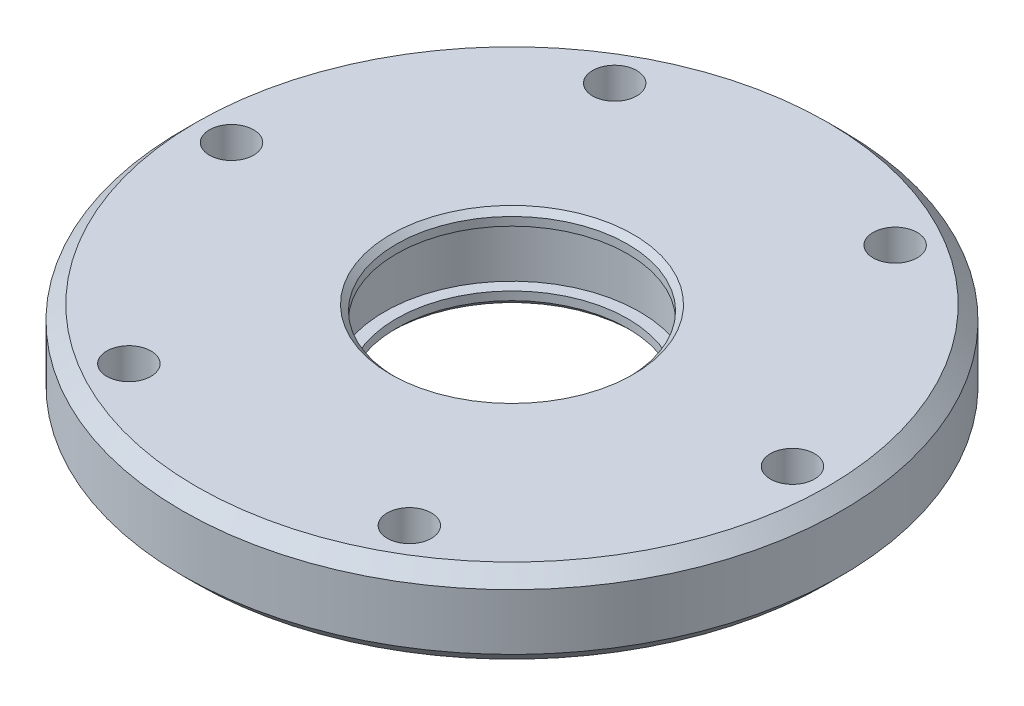
SolidWorks part; units mm, degrees
ref_plane "Front Plane" through (0, 0, 0) normal (0, 0, 1) x (1, 0, 0)
ref_plane "Top Plane" through (0, 0, 0) normal (0, 1, 0) x (1, 0, 0)
ref_plane "Right Plane" through (0, 0, 0) normal (1, 0, 0) x (0, 0, -1)
sketch "Sketch1" plane through (0, 0, 0) normal (0, 1, 0) x (1, 0, 0)
  circle A0 centre (0, 0) radius 20 construction
  circle A1 centre (20, 0) radius 1.575
  circle A2 centre (10, -17.3205) radius 1.575
  circle A3 centre (-10, -17.3205) radius 1.575
  circle A4 centre (-20, 0) radius 1.575
  circle A5 centre (-10, 17.3205) radius 1.575
  circle A6 centre (10, 17.3205) radius 1.575
  circle A7 centre (0, 0) radius 23.5
  circle A8 centre (0, 0) radius 8.25
  point P17 (0, 0)
  dimension "D1" = 40
  dimension "D2" = 3.15
  dimension "D5" = 16.5
  dimension "D4" = 3.5
  dimension "D3" = 6
extrude "Boss-Extrude1" add sketch "Sketch1" along normal mid plane 6
sketch "Sketch2" plane through (0, 0, 0) normal (0, 1, 0) x (1, 0, 0)
  circle A0 centre (0, 0) radius 9.1
  dimension "D1" = 18.2
extrude "Cut-Extrude1" cut sketch "Sketch2" against normal mid plane 4
sketch "Sketch3" plane through (0, -3, 0) normal (0, 1, 0) x (1, 0, 0)
  circle A0 centre (0, 0) radius 18.425
  circle A1 centre (0, 0) radius 21.575
  circle A2 centre (10, 17.3205) radius 1.575 construction
extrude "Boss-Extrude2" add sketch "Sketch3" along normal blind 1
sketch "Sketch4" [suppressed] plane through (0, -3, 0) normal (0, -1, 0) x (1, 0, 0)
  circle A0 centre (0, 0) radius 17.5
  circle A2 centre (0, 0) radius 3.75
  dimension "D1" = 35
  dimension "D2" = 7.5
extrude "Boss-Extrude3" [suppressed] add sketch "Sketch4" along normal blind 10
sketch "Sketch5" [suppressed] plane through (0, -3, 0) normal (0, -1, 0) x (1, 0, 0)
  circle A0 centre (0, 0) radius 19
  circle A1 centre (0, 0) radius 17.5 construction
  circle A2 centre (0, 0) radius 17.5
  dimension "D1" = 1.5
extrude "Boss-Extrude4" [suppressed] add sketch "Sketch5" along normal blind 0.5
chamfer "Chamfer1" distance 1 angle 45 2 edges at (0, -3, 23.5) (0, 3, 23.5)
chamfer "Chamfer2" distance 0.4 angle 45 2 edges at (0, -3, 8.25) (0, 3, 8.25)
chamfer "Chamfer3" [suppressed] distance 0.4 angle 45
sketch "Sketch6" [suppressed] plane through (0, -13, 0) normal (0, -1, 0) x (1, 0, 0)
  circle A0 centre (0, 0) radius 7.5 construction
  circle A1 centre (7.5, 0) radius 2.35
  circle A2 centre (0, 7.5) radius 2.35
  circle A3 centre (-7.5, 0) radius 2.35
  circle A4 centre (0, -7.5) radius 2.35
  dimension "D1" = 15
  dimension "D2" = 4.7
extrude "Cut-Extrude2" [suppressed] cut sketch "Sketch6" against normal blind 4
sketch "Sketch7" [suppressed] plane through (0, -13, 0) normal (0, -1, 0) x (1, 0, 0)
  circle A0 centre (0, 7.5) radius 1.75
  circle A1 centre (7.5, 0) radius 1.75
  circle A2 centre (0, -7.5) radius 1.75
  circle A3 centre (-7.5, 0) radius 1.75
  dimension "D1" = 3.5
extrude "Cut-Extrude3" [suppressed] cut sketch "Sketch7" against normal blind 8
chamfer "Chamfer4" [suppressed] distance 0.4 angle 45
sketch "Sketch8" [suppressed] plane through (0, -3, 0) normal (0, 1, 0) x (1, 0, 0)
  circle A0 centre (0, 0) radius 8.25 construction
  circle A1 centre (0, 0) radius 8.25
extrude "Cut-Extrude4" [suppressed] cut sketch "Sketch8" against normal blind 1
sketch "Sketch9" [suppressed] plane through (0, 3, 0) normal (0, 1, 0) x (1, 0, 0)
  circle A0 centre (0, 0) radius 9.1
  circle A1 centre (0, 0) radius 9.1 construction
extrude "Cut-Extrude5" [suppressed] cut sketch "Sketch9" against normal up to next
chamfer "Chamfer5" [suppressed] distance 0.4 angle 45
equation "\"RotorRadius\"= 26mm"
equation "\"Eccentricity\"= 1.00mm"
equation "\"RollerRadius\"= 1.5mm"
equation "\"GearRatio\"= 10"
equation "\"RollerCount\"=\"GearRatio\" + 1"
equation "\"RotorThickness\"= 6mm"
equation "\"OutputRollerRadius\"= 1.5mm"
equation "\"OutputRollerCount\"= 6"
equation "\"OutputRollerHoleCircleRadius\"=\"RotorRadius\"- 4 * \"OutputRollerRadius\""
equation "\"RotorGap\"= 0.5mm"
equation "\"D1@Sketch1\"=2*\"OutputRollerHoleCircleRadius\""
equation "\"D2@Sketch1\"=\"OutputRollerRadius\"*2+0.15"
equation "\"D1@Boss-Extrude1\"=\"RotorThickness\""
